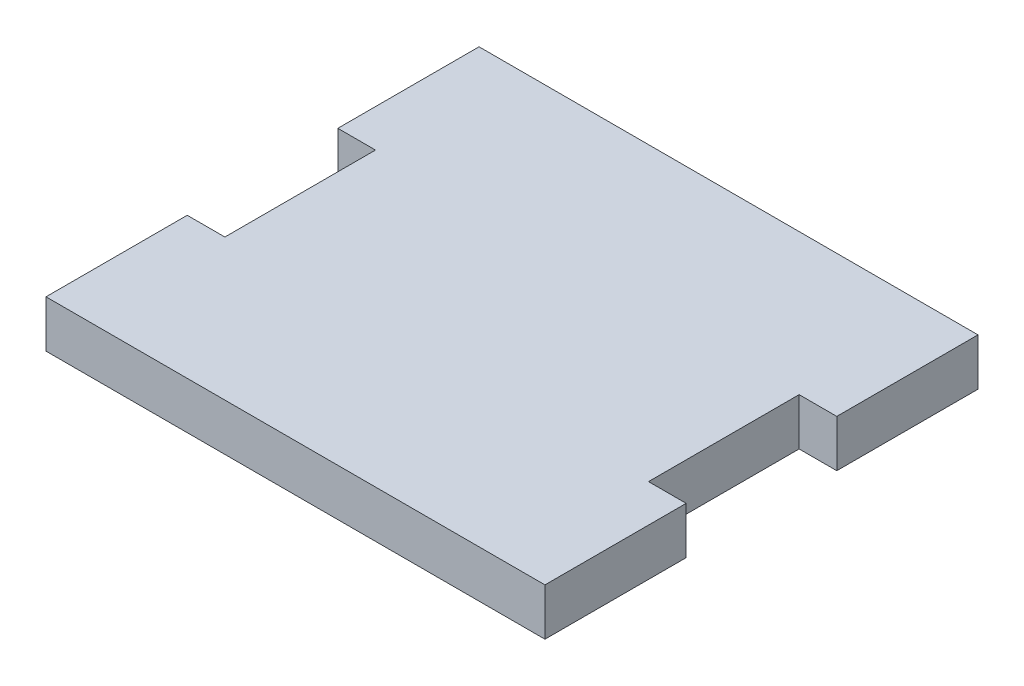
SolidWorks part; units mm, degrees
ref_plane "Front Plane" through (0, 0, 0) normal (0, 0, 1) x (1, 0, 0)
ref_plane "Top Plane" through (0, 0, 0) normal (0, 1, 0) x (1, 0, 0)
ref_plane "Right Plane" through (0, 0, 0) normal (1, 0, 0) x (0, 0, -1)
sketch "Sketch1" plane through (0, 0, 0) normal (0, 1, 0) x (1, 0, 0)
  line L0 (-26.5, 8) -> (-22.5, 8)
  line L1 (-26.5, -23) -> (26.5, -23)
  line L2 (-26.5, -23) -> (-26.5, 23)
  line L3 (-26.5, 23) -> (26.5, 23)
  line L4 (26.5, -23) -> (26.5, 23)
  line L5 (0, 23) -> (0, -23) construction
  line L6 (-26.5, 0) -> (26.5, 0) construction
  line L7 (-22.5, 8) -> (-22.5, -8)
  line L8 (-22.5, -8) -> (-26.5, -8)
  line L9 (26.5, 8) -> (22.5, 8)
  line L10 (22.5, 8) -> (22.5, -8)
  line L11 (22.5, -8) -> (26.5, -8)
  point P64 (0, 0)
  dimension "D1" = 46
  dimension "D2" = 53
  dimension "D3" = 4
  dimension "D4" = 16
  dimension "D5" = 4
  dimension "D6" = 16
  dimension "D7" = 15
  dimension "D8" = 15
extrude "Boss-Extrude1" add sketch "Sketch1" along normal blind 5 contours L11 L10 L9 L4 L3 L2 L0 L7 L8 L1
